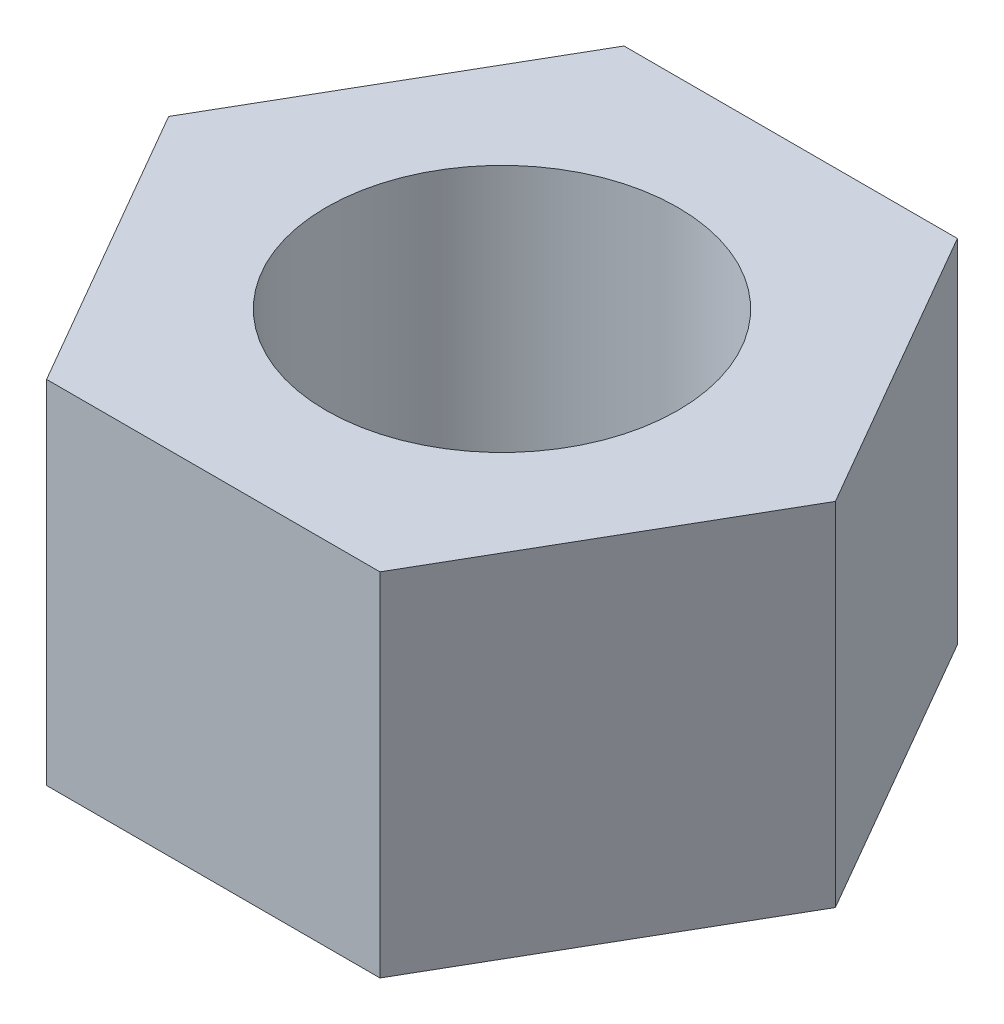
SolidWorks part; units mm, degrees
ref_plane "Front Plane" through (0, 0, 0) normal (0, 0, 1) x (1, 0, 0)
ref_plane "Top Plane" through (0, 0, 0) normal (0, 1, 0) x (1, 0, 0)
ref_plane "Right Plane" through (0, 0, 0) normal (1, 0, 0) x (0, 0, -1)
sketch "Sketch1" plane through (0, 0, 0) normal (0, 1, 0) x (1, 0, 0)
  line L1 (2.8435, 4.925) -> (-2.8435, 4.925)
  line L2 (-2.8435, 4.925) -> (-5.6869, 0)
  line L3 (-5.6869, 0) -> (-2.8435, -4.925)
  line L4 (-2.8435, -4.925) -> (2.8435, -4.925)
  line L5 (2.8435, -4.925) -> (5.6869, 0)
  line L6 (5.6869, 0) -> (2.8435, 4.925)
  circle A0 centre (0, 0) radius 4.925 construction
  circle A1 centre (0, 0) radius 3
  dimension "D2" = 6
  dimension "D1" = 9.85
extrude "Boss-Extrude1" add sketch "Sketch1" along normal blind 6
